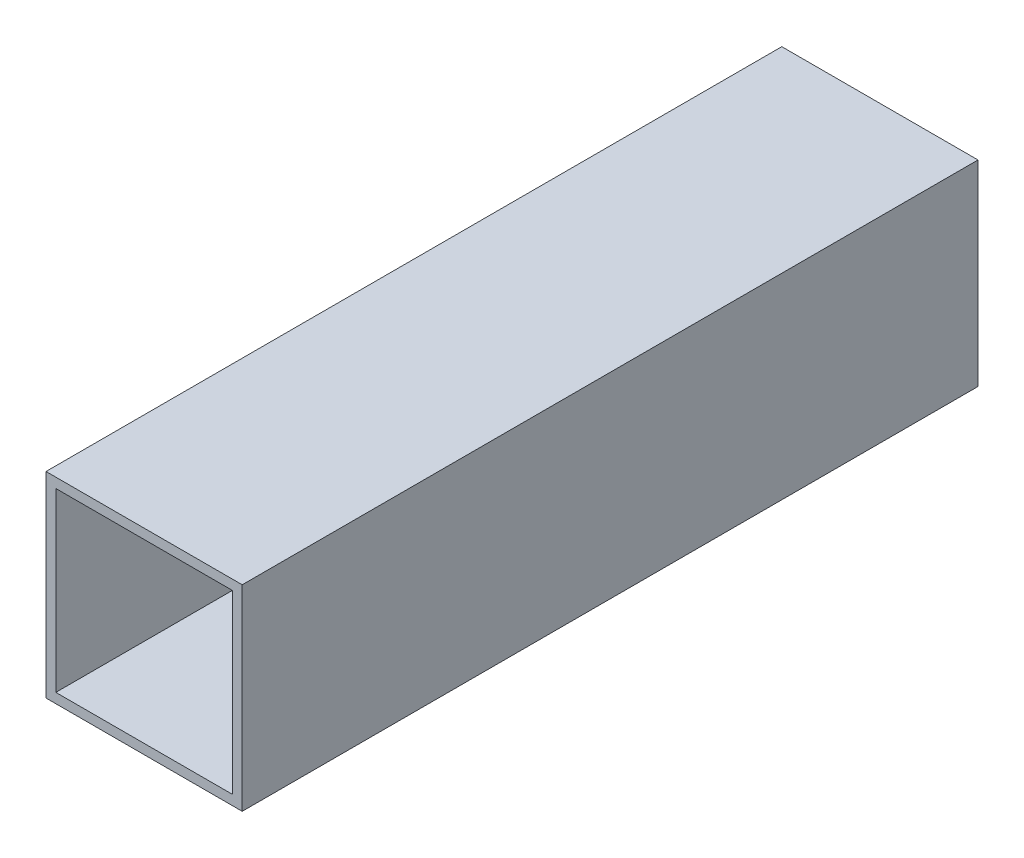
SolidWorks part; units mm, degrees
material "Plain Carbon Steel"
ref_plane "Front Plane" through (0, 0, 0) normal (0, 0, 1) x (1, 0, 0)
ref_plane "Top Plane" through (0, 0, 0) normal (0, 1, 0) x (1, 0, 0)
ref_plane "Right Plane" through (0, 0, 0) normal (1, 0, 0) x (0, 0, -1)
sketch "Sketch1" plane through (0, 0, 0) normal (0, 0, 1) x (1, 0, 0)
  line B0 (-50, -50) -> (50, -50)
  line B1 (-50, -50) -> (-50, 50)
  line B2 (50, -50) -> (50, 50)
  line B3 (-50, 50) -> (50, 50)
  line B4 (-45, -45) -> (45, -45)
  line B5 (-45, -45) -> (-45, 45)
  line B6 (45, -45) -> (45, 45)
  line B7 (-45, 45) -> (45, 45)
sketch_block_instance "10x10x5_profil-1"
sketch_block "10x10x5_profil" parameters "D1"=100, "D2"=100, "D3"=5, "D4"=5
extrude "Boss-Extrude1" add sketch "Sketch1" along normal mid plane 375
